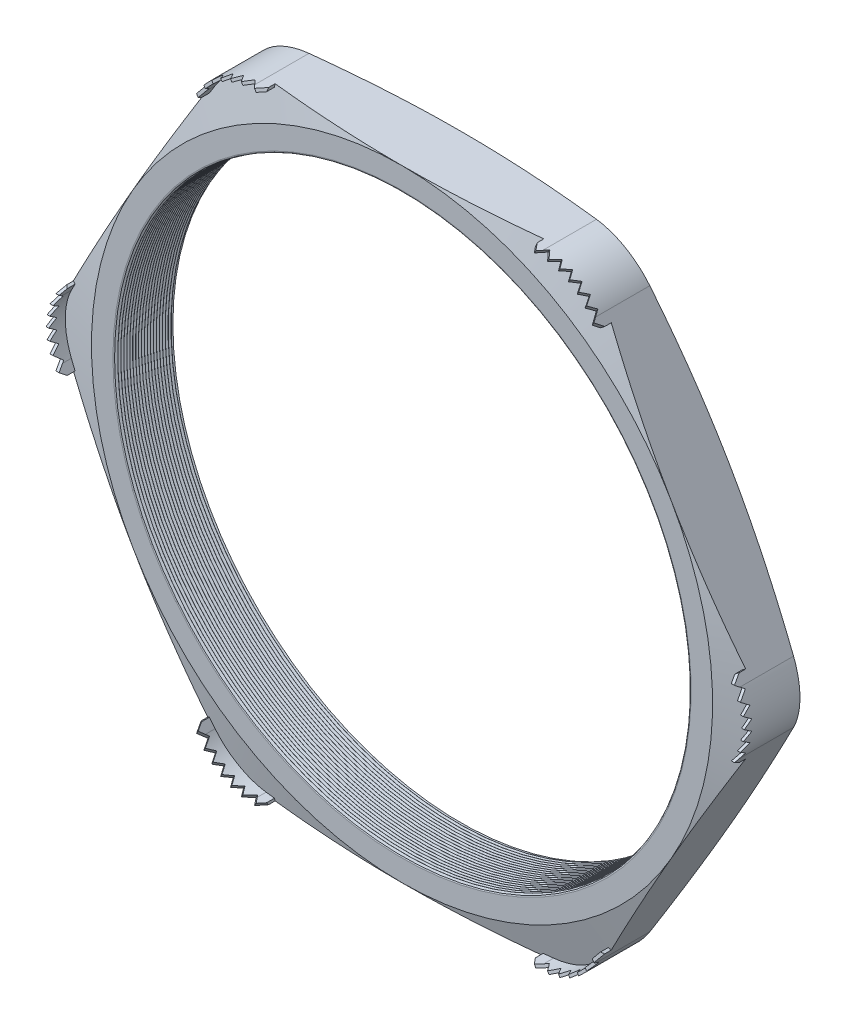
SolidWorks part; units mm, degrees
ref_plane "Front Plane" through (0, 0, 0) normal (0, 0, 1) x (1, 0, 0)
ref_plane "Top Plane" through (0, 0, 0) normal (0, 1, 0) x (1, 0, 0)
ref_plane "Right Plane" through (0, 0, 0) normal (1, 0, 0) x (0, 0, -1)
sketch "Sketch1" plane through (0, 0, 0) normal (0, 0, 1) x (1, 0, 0)
  line L1 (-36.955, 0) -> (-18.4775, -32.004)
  line L2 (-18.4775, -32.004) -> (18.4775, -32.004)
  line L3 (18.4775, -32.004) -> (36.955, 0)
  line L4 (36.955, 0) -> (18.4775, 32.004)
  line L5 (18.4775, 32.004) -> (-18.4775, 32.004)
  line L6 (-18.4775, 32.004) -> (-36.955, 0)
  circle A0 centre (0, 0) radius 32.004 construction
  circle A1 centre (0, 0) radius 29.591
  dimension "TS" = 59.182
  dimension "H" = 64.008
extrude "Extrude1" add sketch "Sketch1" along normal blind 6.096
fillet "Fillet1" radius 6.35 6 edges at (-18.4775, 32.004, 3.048) (-36.955, 0, 3.048) (-18.4775, -32.004, 3.048) (18.4775, -32.004, 3.048) (36.955, 0, 3.048) (18.4775, 32.004, 3.048)
sketch "Sketch2" plane through (0, 0, 6.096) normal (0, 0, 1) x (1, 0, 0)
  line L0 (-14.8113, 32.004) -> (-13.8461, 32.004)
  line L1 (14.8113, 32.004) -> (-14.8113, 32.004) construction
  line L2 (-20.3106, 28.829) -> (-20.7932, 27.9931)
  line L3 (-20.3106, 28.829) -> (-35.1219, 3.175) construction
  line L4 (-14.8113, 31.7246) -> (-13.8461, 31.7246)
  line L5 (-20.0686, 28.6893) -> (-20.5512, 27.8534)
  line L6 (-20.7932, 27.9931) -> (-20.5512, 27.8534)
  line L7 (-13.8461, 32.004) -> (-13.8461, 31.7246)
  arc A0 (-14.8113, 31.7246) -> (-20.0686, 28.6893) centre (-14.8113, 25.654) ccw
  arc A1 (-14.8113, 32.004) -> (-20.3106, 28.829) centre (-14.8113, 25.654) ccw construction
  arc A4 (-14.8113, 32.004) -> (-20.3106, 28.829) centre (-14.8113, 25.654) ccw
  dimension "D1" = 0.9652
  dimension "D2" = 0.9652
  dimension "OFFSET" = 0.2794
fillet "Fillet3" radius 0.2032 2 edges at (29.591, 0, 0) (29.591, 0, 6.096)
sketch "Sketch3" plane through (0, 0, 0) normal (0, 1, 0) x (1, 0, 0)
  line L0 (-29.591, -6.096) -> (-29.591, -5.8027)
  line L2 (-29.591, -5.8027) -> (-29.845, -5.9494)
  line L3 (-29.845, -5.9494) -> (-29.591, -6.096)
  line L4 (-29.591, -0.2032) -> (-29.591, -5.8928) construction
  line L5 (-20.3106, -6.096) -> (-35.1219, -6.096) construction
  dimension "D1" = 60
  dimension "D2" = 60
  dimension "D3" = 0.254
revolve "Cut-Revolve1" cut sketch "Sketch3" angle 360 about axis through (0, 0, 6.096) along (0, 0, -1)
pattern_linear "LPattern1" count 20 spacing 0.3048 along (0, 0, -1) of "Cut-Revolve1"
sketch "Sketch4" plane through (0, 0, 0) normal (0, 0, -1) x (-1, 0, 0)
  line L0 (-35.1219, 3.175) -> (-20.3106, 28.829) construction
  circle A0 centre (0, 0) radius 32.004
extrude "Cut-Extrude1" cut sketch "Sketch4" against normal through all draft 75 flip side to cut
sketch "Sketch5" plane through (0, 0, 6.096) normal (0, 0, 1) x (1, 0, 0)
  line L0 (14.8113, 32.004) -> (-14.8113, 32.004) construction
  circle A0 centre (0, 0) radius 32.004
extrude "Cut-Extrude2" cut sketch "Sketch5" against normal through all draft 75 flip side to cut
extrude "Extrude2" add sketch "Sketch2" along normal blind 1.905 and the other way up to next
ref_plane "Plane1" through (-17.1987, 29.789, 0) normal (0.5, -0.866, 0) x (0.866, 0.5, 0)
sketch "Sketch7" plane through (-17.1987, 29.789, 0) normal (0.5, -0.866, 0) x (0.866, 0.5, 0)
  line L0 (-4.0109, 6.0007) -> (-3.4521, 6.8008)
  line L1 (-4.0109, 5.3278) -> (-4.0109, 8.001) construction
  line L2 (0, 1.3136) -> (0, 4.0135) construction
  line L4 (-3.4521, 6.8008) -> (-2.8933, 6.0007)
  line L5 (-1.1176, 6.8008) -> (-0.5588, 6.0007)
  line L6 (-2.2352, 6.8008) -> (-1.6764, 6.0007)
  line L7 (-0.5588, 6.0007) -> (0, 6.8008)
  line L8 (0, 6.8008) -> (0.5588, 6.0007)
  line L10 (1.1176, 6.8008) -> (1.6764, 6.0007)
  line L11 (2.2352, 6.8008) -> (2.794, 6.0007)
  line L12 (-2.8933, 6.0007) -> (-2.2352, 6.8008)
  line L13 (-1.6764, 6.0007) -> (-1.1176, 6.8008)
  line L14 (0.5588, 6.0007) -> (1.1176, 6.8008)
  line L15 (3.4521, 6.8008) -> (4.0109, 6.0007)
  line L16 (4.0109, 5.3278) -> (4.0109, 8.001) construction
  line L17 (-4.0109, 6.0007) -> (-4.0109, 8.001)
  line L19 (-4.0109, 8.001) -> (4.0109, 8.001)
  line L20 (4.0109, 8.001) -> (4.0109, 6.0007)
  line L23 (1.6764, 6.0007) -> (2.2352, 6.8008)
  line L25 (2.794, 6.0007) -> (3.4521, 6.8008)
  dimension "D1" = 2.0002
  dimension "D2" = 1.2001
  dimension "D3" = 0.5588
extrude "Cut-Extrude4" cut sketch "Sketch7" against normal through all
pattern_circular "CirPattern1" count 6 over 360 about axis through (0, 0, 0) along (0, 0, 1) of "Extrude2"
pattern_circular "CirPattern2" count 6 over 360 about axis through (0, 0, 0) along (0, 0, 1) of "Cut-Extrude4"
